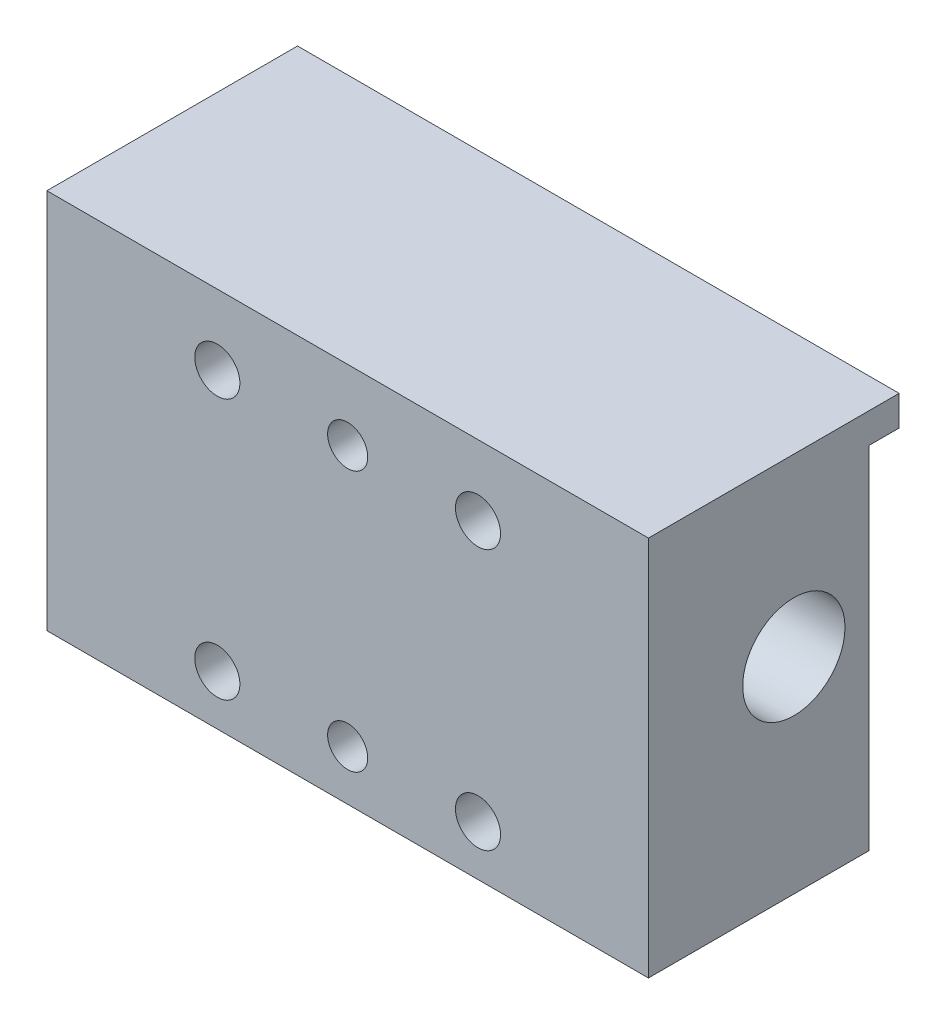
SolidWorks part; units mm, degrees
ref_plane "Alzado" through (0, 0, 0) normal (0, 0, 1) x (1, 0, 0)
ref_plane "Planta" through (0, 0, 0) normal (0, 1, 0) x (1, 0, 0)
ref_plane "Vista lateral" through (0, 0, 0) normal (1, 0, 0) x (0, 0, -1)
sketch "Croquis1" plane through (0, 0, 0) normal (0, 0, 1) x (1, 0, 0)
  line L1 (0, 0) -> (60, 0)
  line L2 (0, 0) -> (0, 38)
  line L3 (0, 38) -> (60, 38)
  line L4 (60, 0) -> (60, 38)
  dimension "D1" = 38
  dimension "D2" = 60
extrude "Saliente-Extruir1" add sketch "Croquis1" along normal blind 22
sketch "Croquis2" plane through (60, 0, 0) normal (1, 0, 0) x (0, 0, -1)
  line L0 (-22, 0) -> (-22, 38) construction
  line L1 (-22, 38) -> (0, 38) construction
  circle A0 centre (-7.5, 20.5) radius 5.1
  dimension "D1" = 10.2
  dimension "D2" = 14.5
  dimension "D3" = 17.5
extrude "Cortar-Extruir1" cut sketch "Croquis2" against normal through all
sketch "Croquis6" plane through (0, 0, 0) normal (0, 0, -1) x (-1, 0, 0)
  line L1 (-60, 35) -> (0, 35)
  line L2 (-60, 35) -> (-60, 38)
  line L3 (-60, 38) -> (0, 38)
  line L4 (0, 35) -> (0, 38)
  dimension "D1" = 3
  dimension "D2" = 60
extrude "Saliente-Extruir2" add sketch "Croquis6" along normal blind 3
hole_wizard "Perforador para roscar para macho de roscar para M33" positions "Croquis10" profile "Croquis11" hole size "M3" standard "DIN"
sketch "Croquis10" plane through (0, 0, 0) normal (-1, 0, 0) x (0, 0, 1)
  line L0 (7.5, 12.5) -> (7.5, 28.5) construction
  line L2 (15.5, 20.5) -> (7.5, 20.5) construction
  circle A0 centre (7.5, 20.5) radius 8 construction
  point P5 (7.5, 12.5)
  point P6 (7.5, 28.5)
  point P8 (15.5, 20.5)
  dimension "D1" = 16
sketch "Croquis11" plane through (0, 20.5, 15.5) normal (0, 1, 0) x (0, 0, 1)
  line L0 (0, 0) -> (0, 14.7511)
  line L1 (0, 14.7511) -> (1.25, 14)
  line L2 (1.25, 14) -> (1.25, 0)
  line L5 (1.25, 0) -> (0, 0)
  line L10 (0, 14.7511) -> (-1.25, 14) construction
  line L11 (0, -6.35) -> (0, 107.95) construction
  dimension "Diámetro de taladro" = 2.5
  dimension "Profundidad de taladro" = 14
  dimension "Ángulo de perforador" = 118
hole_wizard "Taladro de margen para M41" positions "Croquis12" profile "Croquis13" hole size "M4" standard "DIN" end condition through all
sketch "Croquis12" plane through (0, 0, 22) normal (0, 0, 1) x (1, 0, 0)
  line L1 (43, 31) -> (17, 31) construction
  line L2 (43, 31) -> (43, 5) construction
  line L3 (43, 5) -> (17, 5) construction
  line L4 (17, 31) -> (17, 5) construction
  line L5 (43, 31) -> (17, 5) construction
  line L6 (43, 5) -> (17, 31) construction
  line L7 (60, 38) -> (0, 38) construction
  line L8 (0, 38) -> (0, 0) construction
  point P1 (17, 5)
  point P119 (43, 31)
  point P120 (43, 5)
  point P121 (17, 31)
  dimension "D1" = 26
  dimension "D2" = 26
  dimension "D3" = 7
  dimension "D4" = 17
sketch "Croquis13" plane through (17, 5, 22) normal (1, 0, 0) x (0, -1, 0)
  line L0 (0, 0) -> (0, 25)
  line L1 (0, 25) -> (2.25, 25)
  line L2 (2.25, 25) -> (2.25, 0)
  line L5 (2.25, 0) -> (0, 0)
  line L11 (0, -6.35) -> (0, 107.95) construction
  dimension "Diámetro de taladro hasta el siguiente" = 4.5
  dimension "Profundidad de taladro hasta el siguiente" = 25
hole_wizard "Taladros de espiga de Ø4.0mm2" positions "Croquis4" profile "Croquis5" hole size "Ø4.0" standard "DIN"
sketch "Croquis4" plane through (0, 0, 22) normal (0, 0, 1) x (1, 0, 0)
  line L10 (30, 5) -> (30, 31) construction
  line L11 (60, 38) -> (0, 38) construction
  line L12 (0, 38) -> (0, 0) construction
  point P24 (30, 31)
  point P26 (30, 5)
  point P35 (36, 6)
  point P36 (36, 32)
  dimension "D1" = 26
  dimension "D2" = 7
  dimension "D3" = 30
sketch "Croquis5" plane through (30, 31, 22) normal (1, 0, 0) x (0, -1, 0)
  line L0 (0, 0) -> (0, 15.2017)
  line L1 (0, 15.2017) -> (2, 14)
  line L2 (2, 14) -> (2, 0)
  line L5 (2, 0) -> (0, 0)
  line L10 (0, 15.2017) -> (-2, 14) construction
  line L11 (0, -6.35) -> (0, 107.95) construction
  dimension "Diámetro de taladro" = 4
  dimension "Profundidad de taladro" = 14
  dimension "Ángulo de perforador" = 118
